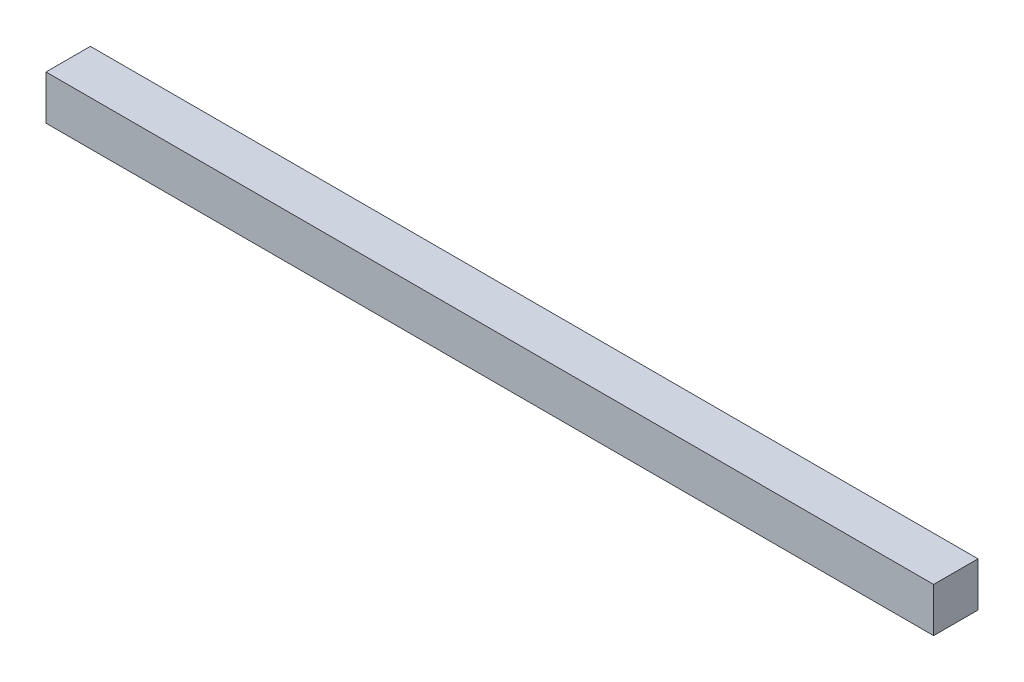
SolidWorks part; units mm, degrees
ref_plane "Front Plane" through (0, 0, 0) normal (0, 0, 1) x (1, 0, 0)
ref_plane "Top Plane" through (0, 0, 0) normal (0, 1, 0) x (1, 0, 0)
ref_plane "Right Plane" through (0, 0, 0) normal (1, 0, 0) x (0, 0, -1)
sketch "Sketch1" plane through (0, 0, 0) normal (0, 0, 1) x (1, 0, 0)
  line L1 (0, 0) -> (200, 0)
  line L2 (0, 0) -> (0, 10)
  line L3 (0, 10) -> (200, 10)
  line L4 (200, 0) -> (200, 10)
  dimension "D1" = 200
  dimension "D2" = 10
extrude "Boss-Extrude1" add sketch "Sketch1" along normal blind 10
